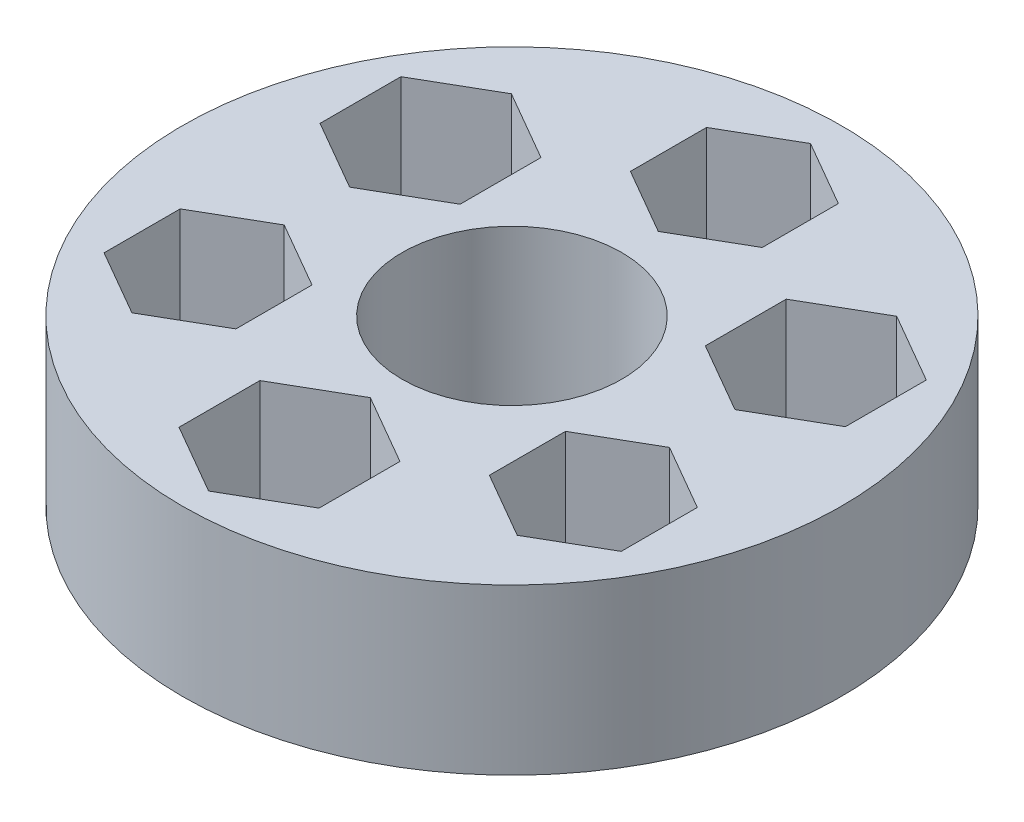
SolidWorks part; units mm, degrees
ref_plane "Alzado" through (0, 0, 0) normal (0, 0, 1) x (1, 0, 0)
ref_plane "Planta" through (0, 0, 0) normal (0, 1, 0) x (1, 0, 0)
ref_plane "Vista lateral" through (0, 0, 0) normal (1, 0, 0) x (0, 0, -1)
sketch "Croquis1" plane through (0, 0, 0) normal (0, 1, 0) x (1, 0, 0)
  circle A0 centre (0, 0) radius 20
  dimension "D1" = 40
extrude "Saliente-Extruir1" add sketch "Croquis1" along normal blind 10
sketch "Croquis2" plane through (0, 10, 0) normal (0, 1, 0) x (1, 0, 0)
  line L0 (7.6913, -4.4406) -> (7.6913, -9.0594)
  line L1 (0, 8.8812) -> (4, 11.1906)
  line L2 (4, 11.1906) -> (4, 15.8094)
  line L3 (4, 15.8094) -> (0, 18.1188)
  line L4 (0, 18.1188) -> (-4, 15.8094)
  line L5 (-4, 15.8094) -> (-4, 11.1906)
  line L6 (-4, 11.1906) -> (0, 8.8812)
  line L7 (7.6913, -9.0594) -> (11.6913, -11.3688)
  line L8 (11.6913, -11.3688) -> (15.6913, -9.0594)
  line L9 (15.6913, -9.0594) -> (15.6913, -4.4406)
  line L10 (15.6913, -4.4406) -> (11.6913, -2.1312)
  line L11 (11.6913, -2.1312) -> (7.6913, -4.4406)
  line L12 (-7.6913, -4.4406) -> (-11.6913, -2.1312)
  line L13 (-11.6913, -2.1312) -> (-15.6913, -4.4406)
  line L14 (-15.6913, -4.4406) -> (-15.6913, -9.0594)
  line L15 (-15.6913, -9.0594) -> (-11.6913, -11.3688)
  line L16 (-11.6913, -11.3688) -> (-7.6913, -9.0594)
  line L17 (-7.6913, -9.0594) -> (-7.6913, -4.4406)
  circle A0 centre (0, 0) radius 13.5
  circle A1 centre (0, 13.5) radius 4 construction
  circle A2 centre (11.6913, -6.75) radius 4 construction
  circle A3 centre (-11.6913, -6.75) radius 4 construction
  point P30 (0, 0)
  dimension "D1" = 27
  dimension "D2" = 8
  dimension "D3" = 3
extrude "Cortar-Extruir1" cut sketch "Croquis2" against normal blind 10 contours L15 L16 L17 L12 L13 L14 | L7 L8 L9 L10 L11 L0 | L6 L1 L2 L3 L4 L5
sketch "Croquis3" plane through (0, 10, 0) normal (0, 1, 0) x (1, 0, 0)
  circle A0 centre (0, 0) radius 6.6657
extrude "Cortar-Extruir2" cut sketch "Croquis3" against normal blind 10
sketch "Croquis4" plane through (0, 10, 0) normal (0, 1, 0) x (1, 0, 0)
  line L0 (-11.6913, 11.6575) -> (-15.9413, 9.2037)
  line L1 (0, -18.4075) -> (4.25, -15.9537)
  line L2 (4.25, -15.9537) -> (4.25, -11.0463)
  line L3 (4.25, -11.0463) -> (0, -8.5925)
  line L4 (0, -8.5925) -> (-4.25, -11.0463)
  line L5 (-4.25, -11.0463) -> (-4.25, -15.9537)
  line L6 (-4.25, -15.9537) -> (0, -18.4075)
  line L7 (-7.4413, 9.2037) -> (-11.6913, 11.6575)
  line L8 (-7.4413, 4.2963) -> (-7.4413, 9.2037)
  line L9 (-11.6913, 1.8425) -> (-7.4413, 4.2963)
  line L10 (-15.9413, 4.2963) -> (-11.6913, 1.8425)
  line L11 (-15.9413, 9.2037) -> (-15.9413, 4.2963)
  line L12 (15.9413, 4.2963) -> (15.9413, 9.2037)
  line L13 (11.6913, 1.8425) -> (15.9413, 4.2963)
  line L14 (7.4413, 4.2963) -> (11.6913, 1.8425)
  line L15 (7.4413, 9.2037) -> (7.4413, 4.2963)
  line L16 (11.6913, 11.6575) -> (7.4413, 9.2037)
  line L17 (15.9413, 9.2037) -> (11.6913, 11.6575)
  circle A0 centre (0, 0) radius 13.5
  circle A1 centre (0, -13.5) radius 4.25 construction
  point P26 (0, 0)
  dimension "D1" = 27
  dimension "D2" = 8.5
  dimension "D3" = 3
extrude "Cortar-Extruir3" cut sketch "Croquis4" against normal blind 10 contours L10 L9 L8 L7 L0 L11 | L14 L13 L12 L17 L16 L15 | L2 L3 L4 L5 L6 L1
